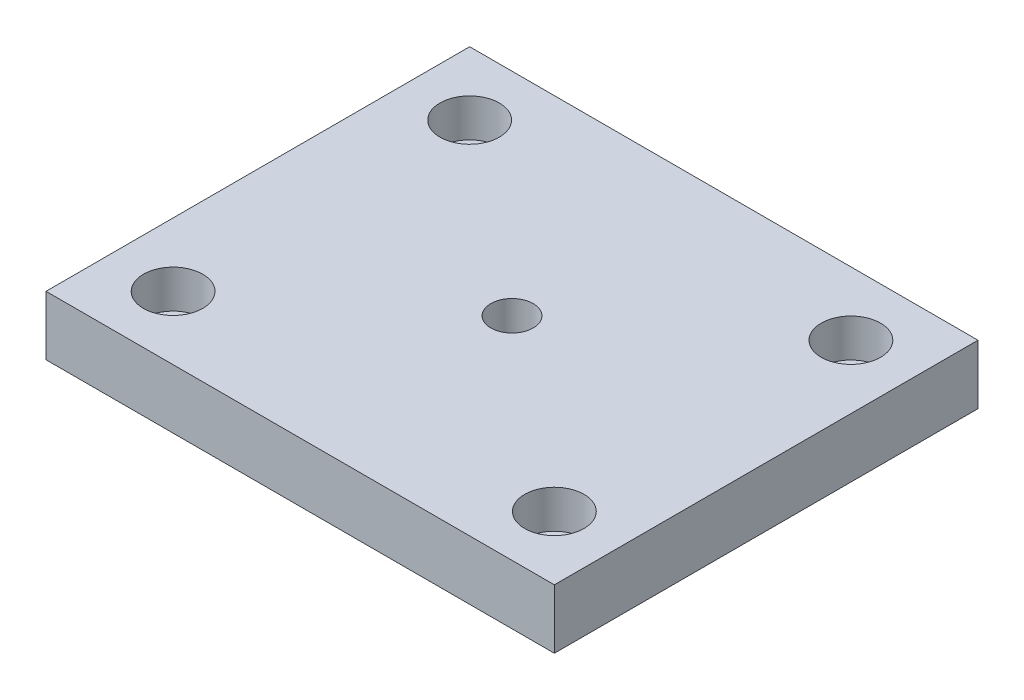
SolidWorks part; units mm, degrees
material "AISI 1020"
ref_plane "Plano frontal" through (0, 0, 0) normal (0, 0, 1) x (1, 0, 0)
ref_plane "Plano superior" through (0, 0, 0) normal (0, 1, 0) x (1, 0, 0)
ref_plane "Plano direito" through (0, 0, 0) normal (1, 0, 0) x (0, 0, -1)
sketch "Esboço1" plane through (0, 0, 0) normal (0, 1, 0) x (1, 0, 0)
  line L1 (-60, -50) -> (60, -50)
  line L2 (-60, -50) -> (-60, 50)
  line L3 (-60, 50) -> (60, 50)
  line L4 (60, -50) -> (60, 50)
  line L5 (-60, -50) -> (60, 50) construction
  line L6 (-60, 50) -> (60, -50) construction
  circle A0 centre (0, 0) radius 5
  point P0 (0, 0)
  dimension "D3" = 10
  dimension "D1" = 120
  dimension "D2" = 100
extrude "Ressalto-extrusão1" add sketch "Esboço1" along normal blind 14
hole_wizard "Rebaixo para SHCS M81" positions "Esboço3" profile "Esboço2" counterbore size "M8" standard "Métrico Ansi" end condition through all
sketch "Esboço3" plane through (0, 14, 0) normal (0, 1, 0) x (-1, 0, 0)
  line L1 (-45, -35) -> (45, -35)
  line L2 (-45, -35) -> (-45, 35)
  line L3 (-45, 35) -> (45, 35)
  line L4 (45, -35) -> (45, 35)
  line L5 (-45, -35) -> (45, 35) construction
  line L6 (-45, 35) -> (45, -35) construction
  point P0 (45, -35)
  point P1 (45, 35)
  point P3 (-45, 35)
  point P5 (-45, -35)
  dimension "D1" = 90
  dimension "D2" = 70
sketch "Esboço2" plane through (-45, 14, -35) normal (1, 0, 0) x (0, 0, 1)
  line L0 (0, 0) -> (0, 14)
  line L1 (0, 14) -> (4.5, 14)
  line L3 (4.5, 14) -> (4.5, 9)
  line L4 (4.5, 9) -> (7, 9)
  line L5 (7, 9) -> (7, 0)
  line L7 (7, 0) -> (0, 0)
  line L11 (0, -6.35) -> (0, 107.95) construction
  dimension "Thru Hole Dia." = 9
  dimension "Thru Hole Depth" = 14
  dimension "C'Bore Dia." = 14
  dimension "C'Bore Depth" = 9
